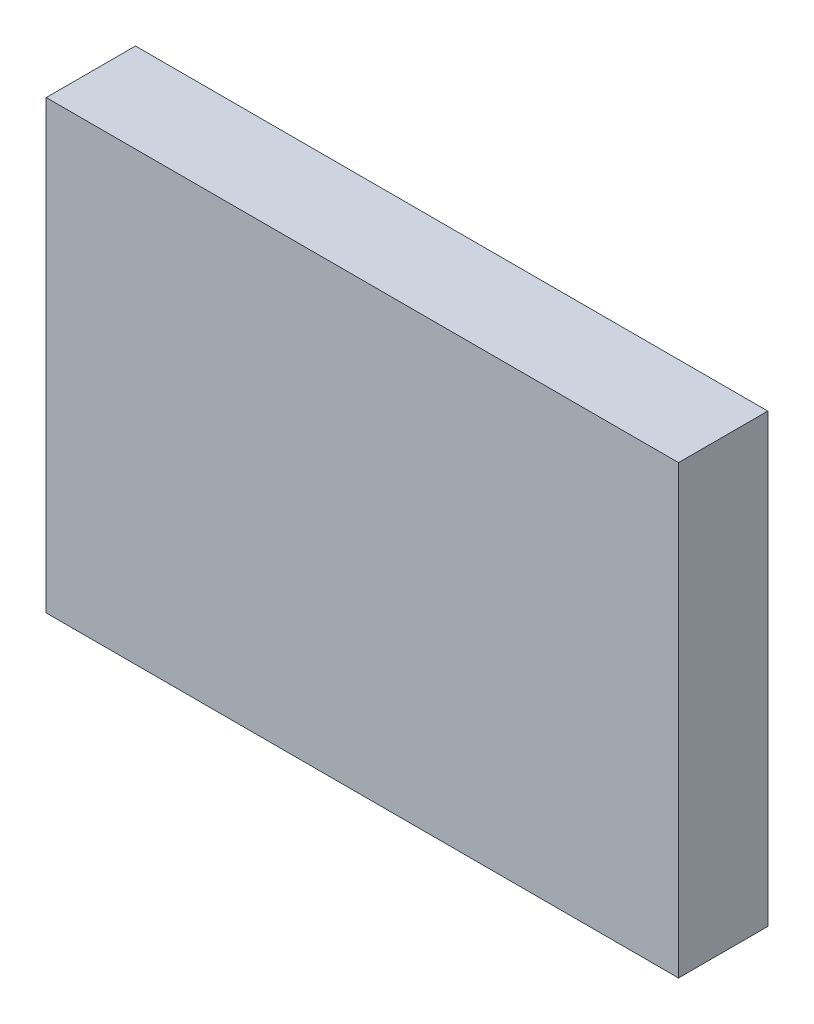
SolidWorks part; units mm, degrees
ref_plane "Plan de face" through (0, 0, 0) normal (0, 0, 1) x (1, 0, 0)
ref_plane "Plan de dessus" through (0, 0, 0) normal (0, 1, 0) x (1, 0, 0)
ref_plane "Plan de droite" through (0, 0, 0) normal (1, 0, 0) x (0, 0, -1)
sketch "Esquisse1" plane through (0, 0, 0) normal (0, 0, 1) x (1, 0, 0)
  line L1 (0, 0) -> (85, 0)
  line L2 (0, 0) -> (0, 60)
  line L3 (0, 60) -> (85, 60)
  line L4 (85, 0) -> (85, 60)
  dimension "D1" = 85
  dimension "D2" = 60
extrude "Boss.-Extru.1" add sketch "Esquisse1" along normal blind 12
